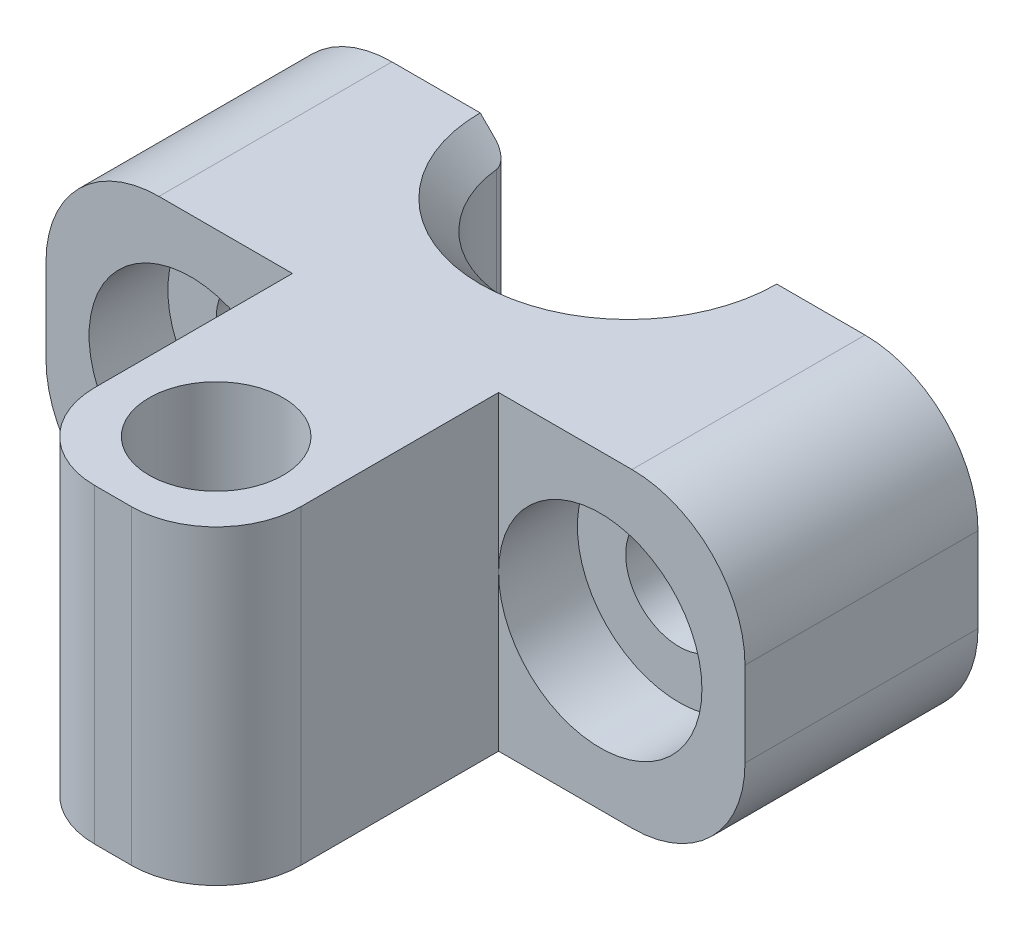
SolidWorks part; units mm, degrees
material "ABS"
ref_plane "Alzado" through (0, 0, 0) normal (0, 0, 1) x (1, 0, 0)
ref_plane "Planta" through (0, 0, 0) normal (0, 1, 0) x (1, 0, 0)
ref_plane "Vista lateral" through (0, 0, 0) normal (1, 0, 0) x (0, 0, -1)
ref_plane "Plano1" through (0, 0, 0) normal (0, 0, -1) x (-1, 0, 0)
sketch "Croquis1" plane through (0, 0, 0) normal (0, 0, -1) x (-1, 0, 0)
  line L0 (-12.375, 5.5) -> (-12.375, -5.5)
  line L1 (-12.375, -5.5) -> (12.375, -5.5)
  line L2 (12.375, -5.5) -> (12.375, 5.5)
  line L3 (12.375, 5.5) -> (-12.375, 5.5)
  point P4 (0, -5.5)
  point P6 (0, 5.5)
  point P7 (12.375, 0)
  point P8 (-12.375, 0)
  dimension "D1" = 11
  dimension "D2" = 24.75
extrude "Saliente-Extruir1" add sketch "Croquis1" against normal blind 8.25
hole_wizard "Refrentado para tornillo con cabeza hexagonal de M3.51" positions "Croquis3" profile "Croquis2" counterbore size "M3.5" standard "Ansi Metric"
sketch "Croquis3" plane through (0, 0, 8.25) normal (0, 0, 1) x (1, 0, 0)
  point P0 (-7.25, 0)
  point P1 (7.25, 0)
sketch "Croquis2" plane through (-7.25, 0, 8.25) normal (1, 0, 0) x (0, -1, 0)
  line L0 (0, 0) -> (0, 8.25)
  line L1 (0, 8.25) -> (1.89, 8.25)
  line L3 (1.89, 8.25) -> (1.89, 2.79)
  line L4 (1.89, 2.79) -> (3.6, 2.79)
  line L5 (3.6, 2.79) -> (3.6, 0)
  line L7 (3.6, 0) -> (0, 0)
  line L11 (0, -6.35) -> (0, 107.95) construction
  dimension "Diámetro de taladro hasta el siguiente" = 3.78
  dimension "Profundidad de taladro hasta el siguiente" = 8.25
  dimension "Diámetro de refrentado" = 7.2
  dimension "Profundidad de refrentado" = 2.79
hole_wizard "Diámetro de taladro Ø8.5 (8.5)1" positions "Croquis5" profile "Croquis4" hole size "Ø8.5" standard "Ansi Metric"
sketch "Croquis5" plane through (0, 5.5, 0) normal (0, 1, 0) x (1, 0, 0)
  point P0 (0, 0)
sketch "Croquis4" plane through (0, 5.5, 0) normal (1, 0, 0) x (0, 0, 1)
  line L0 (0, 0) -> (0, 11)
  line L1 (0, 11) -> (4.25, 11)
  line L2 (4.25, 11) -> (4.25, 0)
  line L5 (4.25, 0) -> (0, 0)
  line L11 (0, -6.35) -> (0, 107.95) construction
  dimension "Diámetro de taladro hasta el siguiente" = 8.5
  dimension "Profundidad de taladro hasta el siguiente" = 11
chamfer "Chaflán1" distance 1 angle 45 2 edges at (0, -5.5, 4.25) (0, 5.5, 4.25)
fillet "Redondeo1" radius 0.5 2 edges at (4.25, 0, 0) (-4.25, 0, 0)
fillet "Redondeo2" radius 4 4 edges at (12.375, -5.5, 4.125) (-12.375, -5.5, 4.125) (12.375, 5.5, 4.125) (-12.375, 5.5, 4.125)
sketch "Croquis6" plane through (0, 0, 8.25) normal (0, 0, 1) x (1, 0, 0)
  line L0 (8.375, -5.5) -> (-8.375, -5.5) construction
  line L1 (3.65, 5.5) -> (-3.65, 5.5)
  line L2 (3.65, 5.5) -> (3.65, -5.5)
  line L3 (3.65, -5.5) -> (-3.65, -5.5)
  line L4 (-3.65, 5.5) -> (-3.65, -5.5)
  line L5 (3.65, 5.5) -> (-3.65, -5.5) construction
  line L6 (3.65, -5.5) -> (-3.65, 5.5) construction
  circle A2 centre (7.25, 0) radius 3.6 construction
  point P0 (0, 0)
extrude "Saliente-Extruir3" add sketch "Croquis6" along normal blind 10 contours L2 L3 L4 L1
sketch "Croquis7" plane through (0, 0, 0) normal (0, 1, 0) x (1, 0, 0)
  line L0 (0, -14.6) -> (3.65, -14.6) construction
  line L1 (3.65, -18.25) -> (3.65, -8.25) construction
  line L2 (0, -14.6) -> (0, -18.25) construction
  line L3 (3.65, -18.25) -> (-3.65, -18.25) construction
  circle A0 centre (0, -14.6) radius 2.375
  dimension "D1" = 4.75
extrude "Cortar-Extruir1" cut sketch "Croquis7" against normal through all both and the other way through all contours A0
fillet "Redondeo3" radius 3 2 edges at (3.65, 0, 18.25) (-3.65, 0, 18.25)
